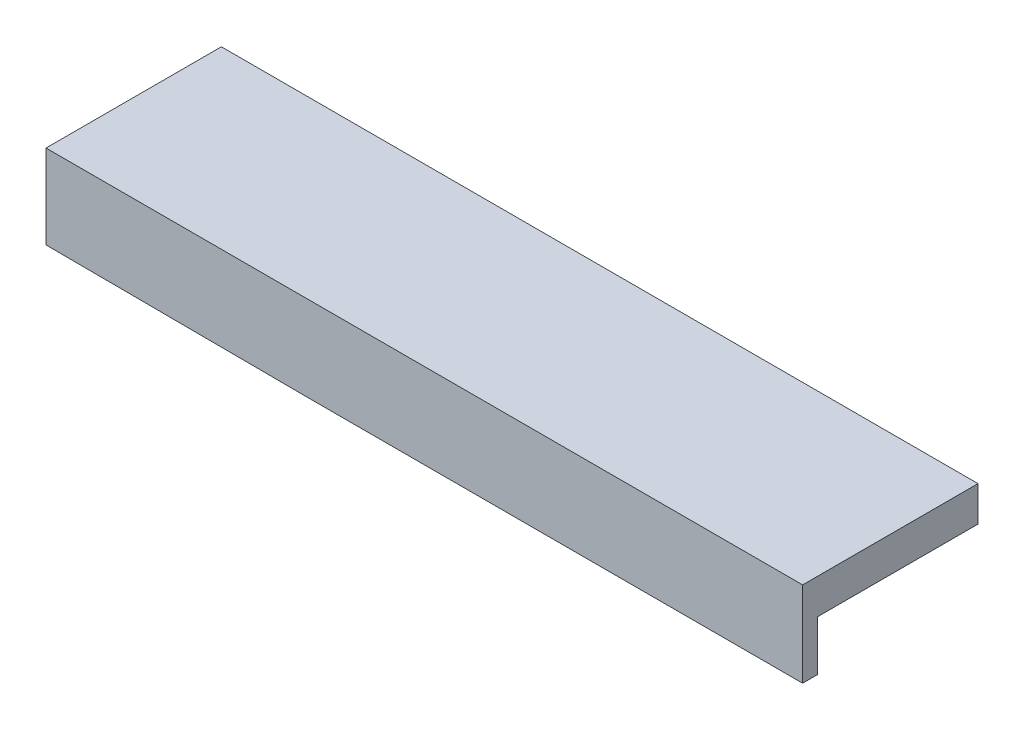
SolidWorks part; units mm, degrees
ref_plane "Front Plane" through (0, 0, 0) normal (0, 0, 1) x (1, 0, 0)
ref_plane "Top Plane" through (0, 0, 0) normal (0, 1, 0) x (1, 0, 0)
ref_plane "Right Plane" through (0, 0, 0) normal (1, 0, 0) x (0, 0, -1)
sketch "Sketch1" plane through (0, 0, 0) normal (0, 0, 1) x (1, 0, 0)
  line L0 (0, 3.5) -> (0, -3.5) construction
  line L1 (-75.5, 3.5) -> (75.5, 3.5)
  line L2 (-75.5, 3.5) -> (-75.5, -3.5)
  line L3 (-75.5, -3.5) -> (-23.1515, -3.5)
  line L4 (75.5, 3.5) -> (75.5, -3.5)
  line L5 (-75.5, 3.5) -> (75.5, -3.5) construction
  line L6 (-75.5, -3.5) -> (75.5, 3.5) construction
  line L7 (17.15, -3.5) -> (17.15, -13.5)
  line L8 (17.15, -13.5) -> (23.15, -13.5)
  line L9 (23.15, -13.5) -> (23.15, -3.5)
  line L10 (-23.2, -13.4999) -> (-23.1515, -3.5)
  line L11 (-17.2, -13.5) -> (-23.2, -13.4999)
  line L12 (-17.15, -3.5) -> (-17.2, -13.5)
  line L13 (-17.15, -3.5) -> (17.15, -3.5)
  line L14 (23.15, -3.5) -> (75.5, -3.5)
  point P0 (0, 0)
  dimension "D1" = 7
  dimension "D2" = 151
  dimension "D3" = 6
  dimension "D4" = 10
  dimension "D5" = 23.15
  dimension "D6" = 10
  dimension "D7" = 6
  dimension "D8" = 23.1515
  dimension "D9" = 46.3015
extrude "Boss-Extrude1" add sketch "Sketch1" along normal blind 35
sketch "Sketch5" plane through (17.15, 0, 0) normal (-1, 0, 0) x (0, 0, 1)
  line L0 (35, -13.5) -> (0, -13.5) construction
  line L1 (35, -3.5) -> (32, -3.5)
  line L2 (35, -3.5) -> (35, -13.5)
  line L3 (35, -13.5) -> (32, -13.5)
  line L4 (32, -3.5) -> (32, -13.5)
  dimension "D1" = 3
extrude "Boss-Extrude2" add sketch "Sketch5" along normal up to surface (34.3 mm away)
sketch "Sketch6" plane through (-23.1339, 0.1123, 0) normal (-1, 0.0049, 0) x (0, 0, 1)
  line L0 (35, -13.6125) -> (0, -13.6125) construction
  line L1 (35, -3.6123) -> (32, -3.6123)
  line L2 (35, -3.6123) -> (35, -13.6125)
  line L3 (35, -13.6125) -> (32, -13.6125)
  line L4 (32, -3.6123) -> (32, -13.6125)
  dimension "D1" = 3
extrude "Boss-Extrude3" add sketch "Sketch6" along normal up to surface (52.3492 mm away)
sketch "Sketch7" plane through (23.15, 0, 0) normal (1, 0, 0) x (0, 0, -1)
  line L0 (-35, -3.5) -> (0, -3.5) construction
  line L1 (-35, -3.5) -> (-32, -3.5)
  line L2 (-35, -3.5) -> (-35, -13.5)
  line L3 (-35, -13.5) -> (-32, -13.5)
  line L4 (-32, -3.5) -> (-32, -13.5)
  line L5 (-35, -13.5) -> (-35, -3.5) construction
  line L6 (-35, -13.5) -> (0, -13.5) construction
  dimension "D1" = 3
extrude "Boss-Extrude4" add sketch "Sketch7" along normal up to surface (52.35 mm away) up to face at (75.5, 0, 17.5)
